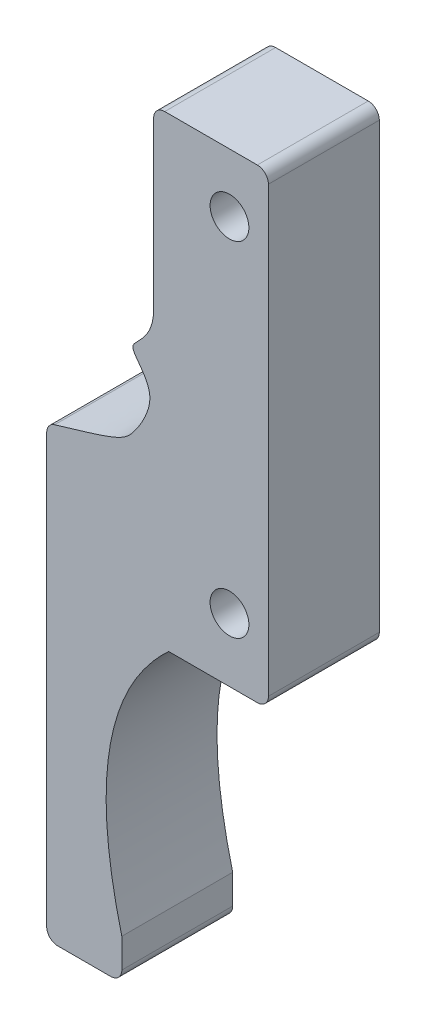
SolidWorks part; units mm, degrees
material "6063-T5"
ref_plane "Front Plane" through (0, 0, 0) normal (0, 0, 1) x (1, 0, 0)
ref_plane "Top Plane" through (0, 0, 0) normal (0, 1, 0) x (1, 0, 0)
ref_plane "Right Plane" through (0, 0, 0) normal (1, 0, 0) x (0, 0, -1)
sketch "Sketch1" plane through (0, 0, 0) normal (0, 0, 1) x (1, 0, 0)
  line L0 (19.5793, 58.738) -> (97.8967, 58.738) construction
  line L2 (41.1958, 130.7586) -> (191.1958, 130.7586) construction
  line L9 (73.0537, 111.9581) -> (81.4075, 111.9581)
  line L10 (82.4075, 110.9581) -> (82.4075, 70.9581)
  line L11 (81.4075, 69.9581) -> (73.4075, 69.9581)
  line L12 (72.0537, 110.9581) -> (72.0537, 96.0191)
  line L13 (62.4075, 81.5662) -> (62.4075, 42.9581)
  line L14 (63.4075, 41.9581) -> (68.1828, 41.9581)
  line L15 (69.1828, 42.9581) -> (69.1828, 45.5999)
  arc A0 (82.4075, 110.9581) -> (81.4075, 111.9581) centre (81.4075, 110.9581) ccw
  arc A1 (73.0537, 111.9581) -> (72.0537, 110.9581) centre (73.0537, 110.9581) ccw
  arc A2 (62.4075, 81.5662) -> (63.1222, 82.5246) centre (63.4075, 81.5662) cw
  arc A3 (63.4075, 41.9581) -> (62.4075, 42.9581) centre (63.4075, 42.9581) cw
  arc A4 (68.1828, 41.9581) -> (69.1828, 42.9581) centre (68.1828, 42.9581) ccw
  arc A5 (81.4075, 69.9581) -> (82.4075, 70.9581) centre (81.4075, 70.9581) ccw
  circle A10 centre (78.8936, 106.673) radius 1.75
  circle A11 centre (78.8936, 75.673) radius 1.75
  spline S0 degree 2 poles (69.1828, 45.5999) (64.9462, 62.1314) (73.4075, 69.9581) knots 0 0 0 1 1 1
  spline S1 degree 3 poles (63.1222, 82.5246) (67.8217, 83.9234) (69.2977, 84.3464) (70.7931, 86.1977) (72.6197, 89.4424) (70.3613, 91.3427) (70.0021, 92.6664) (72.0537, 93.5706) (72.0537, 96.0191) knots 0.01247 0.01247 0.01247 0.01247 0.267446 0.317679 0.514807 0.751762 0.800282 1 1 1 1
  point P21 (82.4075, 69.9581)
  dimension "D2" = 1
  dimension "D3" = 1
  dimension "D4" = 3.5
  dimension "D5" = 3.5
  dimension "D6" = 31
  dimension "D7" = 40
  dimension "D13" = 20
  dimension "D14" = 9
  dimension "D15" = 70
extrude "Boss-Extrude1" add sketch "Sketch1" along normal blind 10
